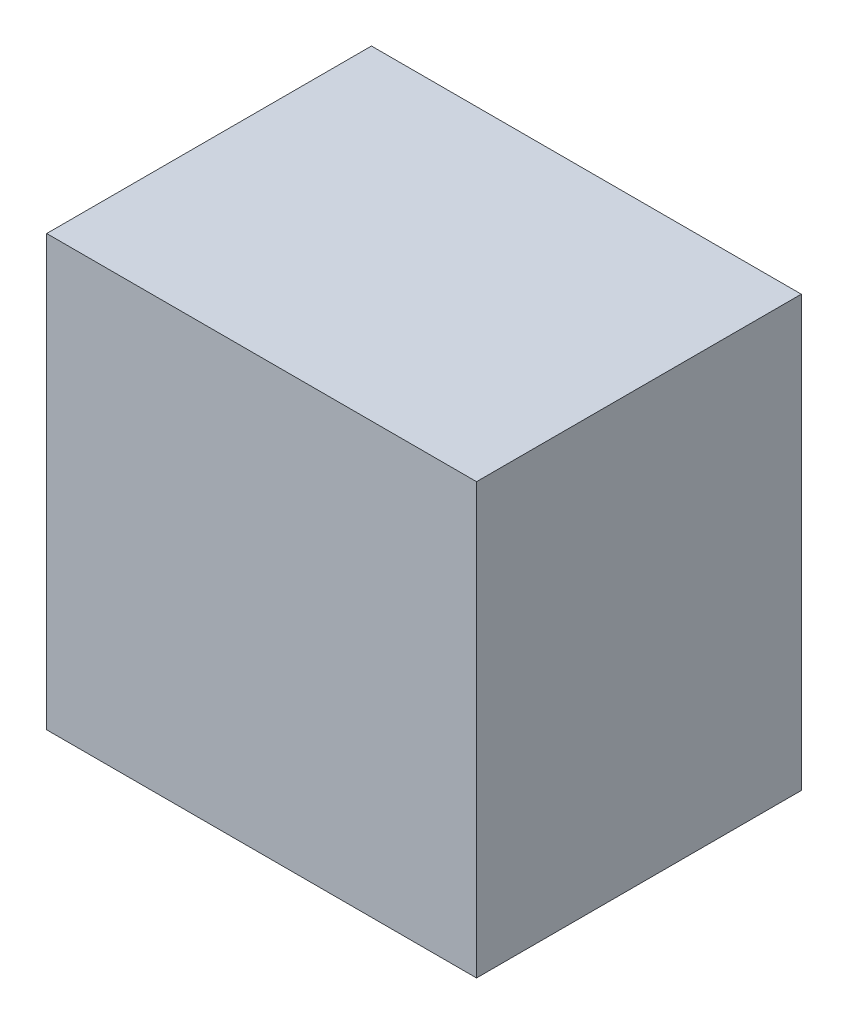
SolidWorks part; units mm, degrees
material "Custom Plastic"
ref_plane "Front Plane" through (0, 0, 0) normal (0, 0, 1) x (1, 0, 0)
ref_plane "Top Plane" through (0, 0, 0) normal (0, 1, 0) x (1, 0, 0)
ref_plane "Right Plane" through (0, 0, 0) normal (1, 0, 0) x (0, 0, -1)
sketch "Sketch1" plane through (0, 0, 0) normal (0, 0, 1) x (1, 0, 0)
  line L1 (-90, 90) -> (90, 90)
  line L2 (-90, 90) -> (-90, -90)
  line L3 (-90, -90) -> (90, -90)
  line L4 (90, 90) -> (90, -90)
  line L5 (-90, 90) -> (90, -90) construction
  line L6 (-90, -90) -> (90, 90) construction
  point P0 (0, 0)
  dimension "D1" = 180
  dimension "D2" = 180
extrude "Boss-Extrude1" add sketch "Sketch1" along normal mid plane 136
